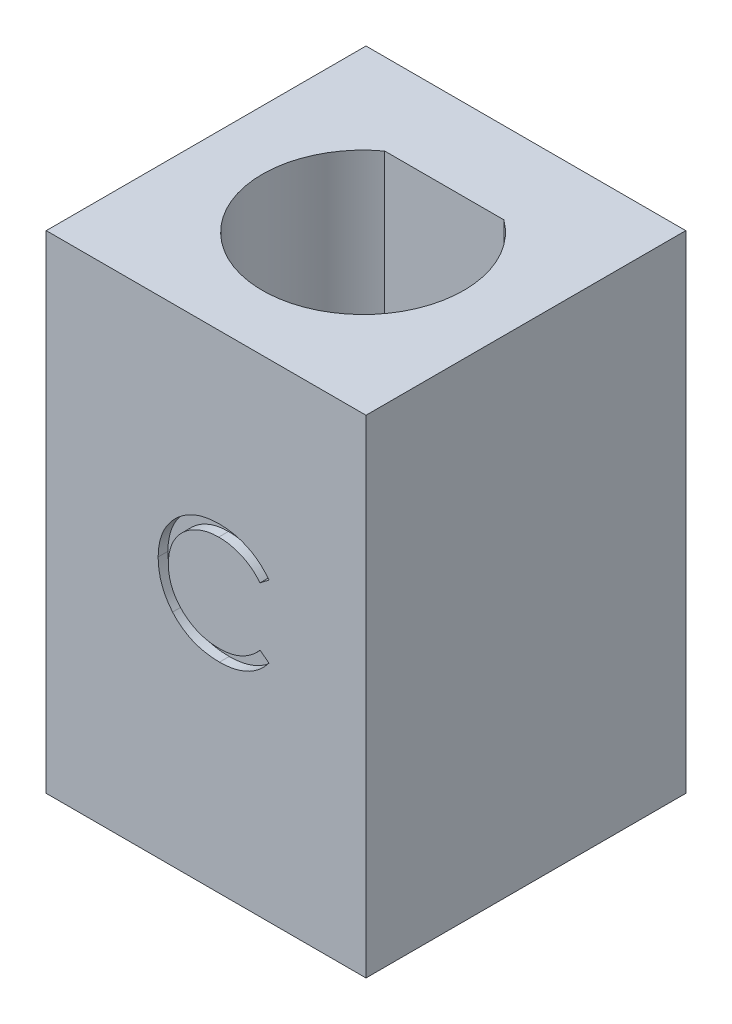
SolidWorks part; units mm, degrees
ref_plane "Front Plane" through (0, 0, 0) normal (0, 0, 1) x (1, 0, 0)
ref_plane "Top Plane" through (0, 0, 0) normal (0, 1, 0) x (1, 0, 0)
ref_plane "Right Plane" through (0, 0, 0) normal (1, 0, 0) x (0, 0, -1)
sketch "Sketch1" plane through (0, 0, 0) normal (0, 1, 0) x (1, 0, 0)
  line L0 (-1.833, 2.4094) -> (1.833, 2.4094)
  line L2 (-4.9207, 4.9207) -> (4.9207, 4.9207)
  line L3 (-4.9207, 4.9207) -> (-4.9207, -4.9207)
  line L4 (-4.9207, -4.9207) -> (4.9207, -4.9207)
  line L5 (4.9207, 4.9207) -> (4.9207, -4.9207)
  arc A1 (-1.833, 2.4094) -> (1.833, 2.4094) centre (0, -0.0906) ccw
  point P2 (0, 0)
  point P3 (0, 2.4094)
  dimension "D1" = 2.5
extrude "Boss-Extrude1" add sketch "Sketch1" along normal blind 15
sketch "Sketch2" plane through (0, 0, 4.9207) normal (0, 0, 1) x (1, 0, 0)
  text T0 "C"
extrude "Cut-Extrude1" cut sketch "Sketch2" against normal blind 0.3
